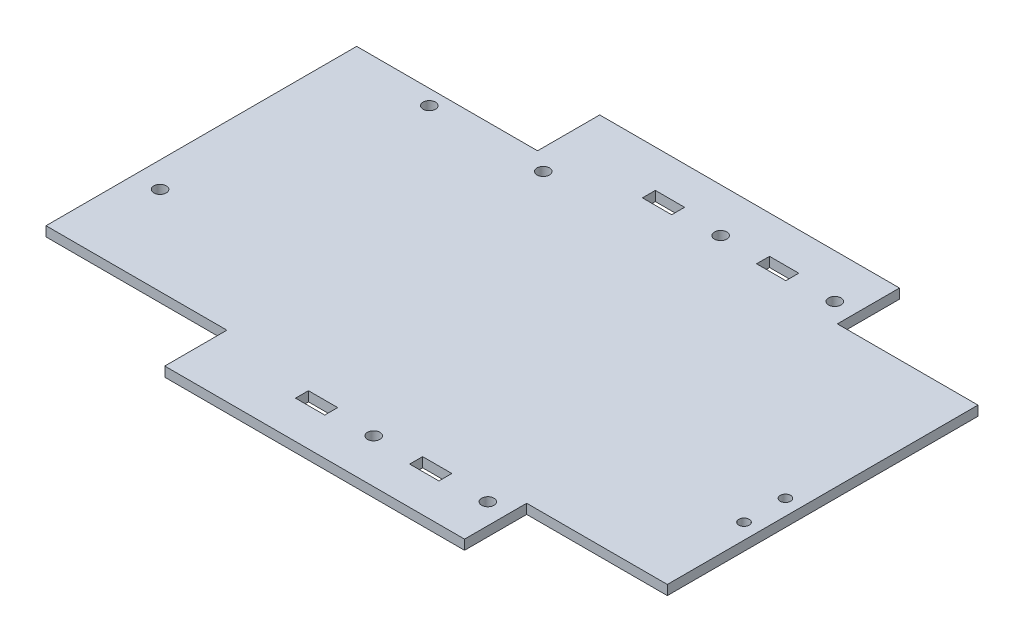
SolidWorks part; units mm, degrees
ref_plane "Front Plane" through (0, 0, 0) normal (0, 0, 1) x (1, 0, 0)
ref_plane "Top Plane" through (0, 0, 0) normal (0, 1, 0) x (1, 0, 0)
ref_plane "Right Plane" through (0, 0, 0) normal (1, 0, 0) x (0, 0, -1)
sketch "Sketch1" plane through (0, 0, 0) normal (0, 0, 1) x (1, 0, 0)
  line L1 (0, 0) -> (152.4, 0)
  line L2 (0, 0) -> (0, 2.3813)
  line L3 (0, 2.3813) -> (152.4, 2.3813)
  line L4 (152.4, 0) -> (152.4, 2.3813)
  dimension "D1" = 2.3813
  dimension "D2" = 152.4
extrude "Boss-Extrude1" add sketch "Sketch1" along normal blind 76.2
hole_wizard "#31 (0.12) Diameter Hole4" positions "Sketch13" profile "Sketch14" hole size "#31" standard "ANSI Inch" end condition through all
sketch "Sketch13" plane through (0, 2.3813, 0) normal (0, 1, 0) x (1, 0, 0)
  line L0 (0, -76.2) -> (0, 0) construction
  line L1 (152.4, 0) -> (0, 0) construction
  line L2 (152.4, -76.2) -> (0, -76.2) construction
  point P0 (49.4486, -3.6901)
  point P2 (21.5086, -3.6901)
  point P4 (6.2686, -54.4901)
  dimension "D1" = 21.5086
  dimension "D2" = 3.6901
  dimension "D3" = 3.6901
  dimension "D4" = 49.4486
  dimension "D5" = 21.7099
  dimension "D6" = 6.2686
sketch "Sketch14" plane through (49.4486, 2.3813, 3.6901) normal (1, 0, 0) x (0, 0, 1)
  line L0 (0, 0) -> (0, 2.3812)
  line L1 (0, 2.3812) -> (1.524, 2.3812)
  line L2 (1.524, 2.3812) -> (1.524, 0)
  line L5 (1.524, 0) -> (0, 0)
  line L11 (0, -6.35) -> (0, 107.95) construction
  dimension "Thru Hole Dia." = 3.048
  dimension "Thru Hole Depth" = 2.3813
sketch "Sketch25" plane through (0, 2.3813, 0) normal (0, 1, 0) x (1, 0, 0)
  line L1 (152.4, 0) -> (0, 0) construction
  line L2 (44.3686, -76.2) -> (117.9016, -76.2)
  line L3 (44.3686, 0) -> (44.3686, 8.89)
  line L4 (44.3686, 8.89) -> (117.9016, 8.89)
  line L5 (117.9016, 8.89) -> (117.9016, 0)
  line L6 (0, -38.1) -> (152.4, -38.1) construction
  line L7 (0, -76.2) -> (0, 0) construction
  line L8 (152.4, -76.2) -> (152.4, 0) construction
  line L9 (117.9016, -85.09) -> (117.9016, -76.2)
  line L10 (44.3686, -85.09) -> (117.9016, -85.09)
  line L11 (44.3686, -76.2) -> (44.3686, -85.09)
  line L12 (44.3686, -76.2) -> (44.3686, -85.09)
  line L13 (44.3686, -85.09) -> (117.9016, -85.09)
  line L14 (117.9016, -76.2) -> (117.9016, -85.09)
  line L15 (44.3686, 0) -> (117.9016, 0)
  line L16 (44.3686, 0) -> (44.3686, 8.89)
  line L17 (44.3686, 8.89) -> (117.9016, 8.89)
  line L18 (117.9016, 0) -> (117.9016, 8.89)
  line M29 (152.4, 0) -> (0, 0)
  line M31 (0, -76.2) -> (152.4, -76.2)
  dimension "D1" = 73.533
  dimension "D5" = 8.89
extrude "Boss-Extrude2" add sketch "Sketch25" against normal up to surface (2.3813 mm away) contours L5 L4 L3 M29 | L11 L10 L9 M31 up to face at (49.4486, 0, 5.2141)
sketch "Sketch26" plane through (0, 2.3813, 0) normal (0, 1, 0) x (1, 0, 0)
  line L0 (81.1351, 8.89) -> (81.1351, -85.09) construction
  line L1 (44.3686, 8.89) -> (117.9016, 8.89) construction
  line L2 (44.3686, -85.09) -> (117.9016, -85.09) construction
  line L3 (0, -38.1) -> (152.4, -38.1) construction
  line L4 (0, -76.2) -> (0, 0) construction
  line L5 (152.4, -76.2) -> (152.4, 0) construction
  line L7 (44.3686, 0) -> (44.3686, 8.89) construction
  line L8 (67.2286, 6.0325) -> (74.4041, 6.0325)
  line L9 (67.2286, 6.0325) -> (67.2286, 2.8575)
  line L10 (67.2286, 2.8575) -> (74.4041, 2.8575)
  line L11 (74.4041, 6.0325) -> (74.4041, 2.8575)
  line L14 (95.2321, 6.0325) -> (102.4076, 6.0325)
  line L15 (95.2321, 6.0325) -> (95.2321, 2.8575)
  line L16 (95.2321, 2.8575) -> (102.4076, 2.8575)
  line L17 (102.4076, 6.0325) -> (102.4076, 2.8575)
  line L19 (95.2321, -79.0575) -> (102.4076, -79.0575)
  line L20 (102.4076, -82.2325) -> (102.4076, -79.0575)
  line L21 (95.2321, -82.2325) -> (102.4076, -82.2325)
  line L22 (95.2321, -82.2325) -> (95.2321, -79.0575)
  line L23 (67.2286, -82.2325) -> (74.4041, -82.2325)
  line L24 (67.2286, -82.2325) -> (67.2286, -79.0575)
  line L25 (74.4041, -82.2325) -> (74.4041, -79.0575)
  line L26 (67.2286, -79.0575) -> (74.4041, -79.0575)
  point P12 (67.2286, 4.445)
  point P19 (44.3686, 4.445)
  dimension "D1" = 0
  dimension "D2" = 3.175
  dimension "D3" = 7.1755
  dimension "D4" = 81.915
  dimension "D5" = 6.731
  dimension "D6" = 3.175
  dimension "D7" = 7.1755
  dimension "D9" = 14.097
extrude "Cut-Extrude3" cut sketch "Sketch26" against normal through all
hole_wizard "#31 (0.12) Diameter Hole6" positions "Sketch29" profile "Sketch30" hole size "#31" standard "ANSI Inch" end condition through all
sketch "Sketch29" plane through (0, 2.3813, 0) normal (0, 1, 0) x (1, 0, 0)
  line L0 (74.4041, 2.8575) -> (74.4041, 6.0325) construction
  line L1 (102.4076, 2.8575) -> (102.4076, 6.0325) construction
  line L2 (74.4041, -82.2325) -> (74.4041, -79.0575) construction
  line L3 (102.4076, -82.2325) -> (102.4076, -79.0575) construction
  point P0 (84.8181, 4.445)
  point P2 (112.8216, 4.445)
  point P4 (112.8216, -80.645)
  point P6 (84.8181, -80.645)
  dimension "D1" = 10.414
  dimension "D2" = 10.414
  dimension "D3" = 10.414
  dimension "D4" = 10.414
sketch "Sketch30" plane through (84.8181, 2.3813, -4.445) normal (1, 0, 0) x (0, 0, 1)
  line L0 (0, 0) -> (0, 2.3812)
  line L1 (0, 2.3812) -> (1.524, 2.3812)
  line L2 (1.524, 2.3812) -> (1.524, 0)
  line L5 (1.524, 0) -> (0, 0)
  line L11 (0, -6.35) -> (0, 107.95) construction
  dimension "Thru Hole Dia." = 3.048
  dimension "Thru Hole Depth" = 2.3813
sketch "Sketch31" plane through (0, 0, 0) normal (0, -1, 0) x (-1, 0, 0)
  line L0 (-152.4, -38.1) -> (-148.59, -38.1)
  line L1 (-152.4, -76.2) -> (-152.4, 0) construction
  line L2 (-148.59, -38.1) -> (-148.59, -43.4216)
  line L3 (-148.59, -38.1) -> (-148.59, -33.02)
  line L4 (-102.4076, -79.0575) -> (-95.2321, -79.0575)
  line L5 (-148.59, -43.4216) -> (-148.59, -53.5816)
  circle A1 centre (-148.59, -43.4216) radius 1.27
  circle A2 centre (-148.59, -53.5816) radius 1.27
  dimension "D2" = 5.08
  dimension "D1" = 3.81
  dimension "D3" = 7.1755
  dimension "D4" = 10.16
sketch "Sketch32" plane through (0, 0, 0) normal (0, -1, 0) x (1, 0, 0)
  line L0 (44.3686, 85.09) -> (44.3686, 91.44)
  line L1 (44.3686, 91.44) -> (117.9016, 91.44)
  line L2 (117.9016, 91.44) -> (117.9016, 85.09)
  line L3 (44.3686, -8.89) -> (44.3686, -15.24)
  line L4 (44.3686, -15.24) -> (117.9016, -15.24)
  line L5 (117.9016, -15.24) -> (117.9016, -8.89)
  line L6 (44.3686, 85.09) -> (117.9016, 85.09)
  line L7 (44.3686, -8.89) -> (117.9016, -8.89)
  dimension "D1" = 6.35
  dimension "D2" = 6.35
extrude "Boss-Extrude3" add sketch "Sketch32" against normal blind 2.3813
extrude "Cut-Extrude4" cut sketch "Sketch31" against normal through all
